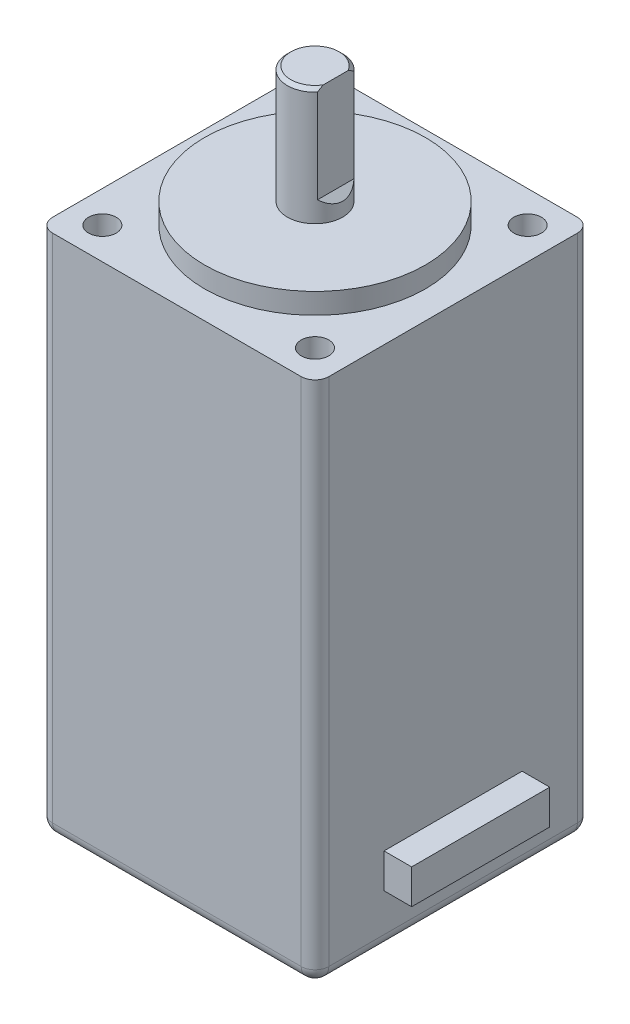
SolidWorks part; units mm, degrees
ref_plane "Front Plane" through (0, 0, 0) normal (0, 0, 1) x (1, 0, 0)
ref_plane "Top Plane" through (0, 0, 0) normal (0, 1, 0) x (1, 0, 0)
ref_plane "Right Plane" through (0, 0, 0) normal (1, 0, 0) x (0, 0, -1)
sketch "Sketch1" plane through (0, 0, 0) normal (0, 1, 0) x (1, 0, 0)
  line L1 (10, -10) -> (-10, -10)
  line L2 (10, -10) -> (10, 10)
  line L3 (10, 10) -> (-10, 10)
  line L4 (-10, -10) -> (-10, 10)
  line L5 (10, -10) -> (-10, 10) construction
  line L6 (10, 10) -> (-10, -10) construction
  point P0 (0, 0)
  dimension "D1" = 20
extrude "Boss-Extrude1" add sketch "Sketch1" against normal blind 38
sketch "Sketch2" plane through (0, 0, 0) normal (0, 1, 0) x (1, 0, 0)
  line L1 (7.7, -7.7) -> (-7.7, -7.7) construction
  line L2 (7.7, -7.7) -> (7.7, 7.7) construction
  line L3 (7.7, 7.7) -> (-7.7, 7.7) construction
  line L4 (-7.7, -7.7) -> (-7.7, 7.7) construction
  line L5 (7.7, -7.7) -> (-7.7, 7.7) construction
  line L6 (7.7, 7.7) -> (-7.7, -7.7) construction
  circle A0 centre (-7.7, 7.7) radius 1
  circle A1 centre (7.7, 7.7) radius 1
  circle A2 centre (7.7, -7.7) radius 1
  circle A3 centre (-7.7, -7.7) radius 1
  point P0 (0, 0)
  dimension "D4" = 2
  dimension "D2" = 15.4
extrude "Cut-Extrude1" cut sketch "Sketch2" against normal blind 2.5
sketch "Sketch3" plane through (0, 0, 0) normal (0, 1, 0) x (1, 0, 0)
  circle A0 centre (0, 0) radius 8
  dimension "D1" = 16
extrude "Boss-Extrude2" add sketch "Sketch3" along normal blind 1.5
sketch "Sketch4" plane through (0, 0, 0) normal (0, 1, 0) x (1, 0, 0)
  circle A0 centre (0, 0) radius 2
  dimension "D1" = 4
extrude "Boss-Extrude3" add sketch "Sketch4" along normal blind 10
sketch "Sketch5" plane through (0, 0, 0) normal (0, 0, 1) x (1, 0, 0)
  line L0 (2, 10) -> (1.5, 10)
  line L1 (2, 10) -> (-2, 10) construction
  line L2 (1.5, 10) -> (1.5, 3)
  line L3 (1.5, 3) -> (2, 2.5)
  line L4 (2, 1.5) -> (2, 10) construction
  line L5 (2, 2.5) -> (2, 10)
  dimension "D1" = 45
  dimension "D2" = 0.5
  dimension "D3" = 7.5
extrude "Cut-Extrude2" cut sketch "Sketch5" against normal through all both and the other way through all
chamfer "Chamfer1" distance 0.25 angle 45 1 edges at (-2, 10, 0)
fillet "Fillet1" radius 1 8 edges at (0, -38, 10) (10, -38, 0) (0, -38, -10) (-10, -38, 0) (-10, -19, -10) (10, -19, -10) (10, -19, 10) (-10, -19, 10)
sketch "Sketch6" plane through (0, 0, 0) normal (1, 0, 0) x (0, 0, -1)
  line L0 (0, -33) -> (0, 0) construction
  line L1 (5, -34.25) -> (-5, -34.25)
  line L2 (5, -34.25) -> (5, -31.75)
  line L3 (5, -31.75) -> (-5, -31.75)
  line L4 (-5, -34.25) -> (-5, -31.75)
  line L5 (5, -34.25) -> (-5, -31.75) construction
  line L6 (5, -31.75) -> (-5, -34.25) construction
  line L7 (9, -38) -> (-9, -38) construction
  point P0 (0, -33)
  dimension "D1" = 5
  dimension "D2" = 2.5
  dimension "D3" = 10
extrude "Boss-Extrude4" add sketch "Sketch6" along normal offset from surface (12 mm away) 2 up to face at (10, -18.5, 0) offset beyond the face yes
equation "\"D1@Sketch1\" = \"ARM Both Nema Width\""
equation "\"D1@Boss-Extrude1\" = \"ARM Both Nema Height\""
equation "\"D2@Sketch2\" = \"ARM Both Nema Bolt Off\""
equation "\"D4@Sketch2\" = \"ARM Both Nema Bolt Size\""
equation "\"D1@Cut-Extrude1\" = \"ARM Both Nema Bolt Depth\""
equation "\"D1@Sketch3\" = \"ARM Both Nema Center Dia 1\" - 1.0mm"
equation "\"D1@Boss-Extrude2\" = \"ARM Both Nema Center Height\""
equation "\"D1@Sketch4\" = \"ARM Both Nema Shaft Dia\""
equation "\"D1@Boss-Extrude3\"= \"ARM Both Nema Shaft Length\""
equation "\"D2@Sketch5\"= \"ARM Both Nema Shaft Dia\" * ( 1 / 8 )"
equation "\"D3@Sketch5\"= \"ARM Both Nema Shaft Length\" * ( 3 / 4 )"
equation "\"D1@Chamfer1\"= \"ALL Small Fillet\" / 2"
equation "\"ALL Big Fillet\"= 10.0mm"
equation "\"ALL Medium Fillet\"= 1.0mm"
equation "\"ALL Small Fillet\"= 0.5mm"
equation "\"BODY Rad\"= 82.5mm"
equation "\"BODY End Cut Rad\"= 72.5mm"
equation "\"BODY Height Ext\"= 27.5mm"
equation "\"BODY Bottom Cut Dist\"= 50.0mm"
equation "\"BODY Seal Thickness\"= 3.75mm"
equation "\"BODY Wall Extra Thickness\"= 2.5mm"
equation "\"BODY Bottom Extra Nut Wall\"= 7.5mm"
equation "\"ARM Both Dia\"= 39.75mm"
equation "\"ARM Both Length\"= 67.5mm"
equation "\"ARM Both Wire Hole Dia\"= 15.0mm"
equation "\"ARM Both Prop Seal Thickness\"= 2.5mm"
equation "\"ARM Both Brass Insert Dia\"= 4.875mm"
equation "\"ARM Both Bolt Cut Depth\"= 12.5mm"
equation "\"ARM Both Nema Bolt Off\"= 15.4mm"
equation "\"ARM Both Nema Bolt Depth\"= 2.5mm"
equation "\"ARM Both Nema Width\"= 20.0mm"
equation "\"ARM Both Nema Wall Off\"= 2.5mm"
equation "\"ARM Both Nema Center Dia 1\"= 17.0mm"
equation "\"ARM Both Nema Center Dia 2\"= 10.0mm"
equation "\"ARM Both Nema Bearing OD\"= 16.0mm"
equation "\"ARM Both Nema Bearing ID\"= 10.0mm"
equation "\"ARM Both Nema Bearing Thickness\"= 4.0mm"
equation "\"ARM Both Nema Height\"= 38.0mm"
equation "\"ARM Both Nema Shaft Dia\"= 4.0mm"
equation "\"ARM Both Nema Shaft Length\"= 10.0mm"
equation "\"ARM Both Nema Center Height\"= 1.5mm"
equation "\"ARM Rotating Bearing OD\"= 68.0mm"
equation "\"ARM Rotating Bearing ID\"= 40.0mm"
equation "\"ARM Rotating Bearing Thickness\"= 15.0mm"
equation "\"ARM Static Mount Dia\"= 65.0mm"
equation "\"ARM Static Bolt Off\"= 1.125mm"
equation "\"ALL Bolt Hole Off\"= 0.25mm"
equation "\"ALL Vert Bolt Hole Off Scalar\"= 0.5mm"
equation "\"ALL Horz Bolt Hole Off Scalar\"= 1.25mm"
equation "\"ALL Nut Size Off\"= 0.25mm"
equation "\"ALL Vert Nut Off Scalar\"= 0.5mm"
equation "\"ALL Horz Nut Off Scalar\"= 1.25mm"
equation "\"BODY Bolt Count\"= 12"
equation "\"BODY Bolt Size\"= 6"
equation "\"BODY Bolt Length\"= 22.0mm"
equation "\"BODY Bolt Head Dia\"= IIF ( \"BODY Bolt Size\" = 3 , 5.75mm , IIF ( \"BODY Bolt Size\" = 4 , 7.25mm , IIF ( \"BODY Bolt Size\" = 5 , 8.75mm , IIF ( \"BODY Bolt Size\" = 6 , 10.25mm , 5.75mm ) ) ) )"
equation "\"BODY Bolt Head Height\"= IIF ( \"BODY Bolt Size\" = 3 , 3.0mm , IIF ( \"BODY Bolt Size\" = 4 , 4.0mm , IIF ( \"BODY Bolt Size\" = 5 , 5.0mm , IIF ( \"BODY Bolt Size\" = 6 , 6.0mm , 3.0mm ) ) ) )"
equation "\"BODY Nut Width\"= IIF ( \"BODY Bolt Size\" = 3 , 5.5mm , IIF ( \"BODY Bolt Size\" = 4 , 7.0mm , IIF ( \"BODY Bolt Size\" = 5 , 8.0mm , IIF ( \"BODY Bolt Size\" = 6 , 10.0mm , 5.5mm ) ) ) )"
equation "\"BODY Nut Height\"= IIF ( \"BODY Bolt Size\" = 3 , 4.0mm , IIF ( \"BODY Bolt Size\" = 4 , 5.0mm , IIF ( \"BODY Bolt Size\" = 5 , 5.0mm , IIF ( \"BODY Bolt Size\" = 6 , 6.0mm , 4.0mm ) ) ) )"
equation "\"ARM Static Bolt Count\"= 8"
equation "\"ARM Static Bolt Size\"= 5"
equation "\"ARM Static Bolt Length\"= 20.0mm"
equation "\"ARM Static Bolt Head Dia\"= IIF ( \"ARM Static Bolt Size\" = 3 , 5.75mm , IIF ( \"ARM Static Bolt Size\" = 4 , 7.25mm , IIF ( \"ARM Static Bolt Size\" = 5 , 8.75mm , IIF ( \"ARM Static Bolt Size\" = 6 , 10.25mm , 5.75mm ) ) ) )"
equation "\"ARM Static Bolt Head Height\"= IIF ( \"ARM Static Bolt Size\" = 3 , 3.0mm , IIF ( \"ARM Static Bolt Size\" = 4 , 4.0mm , IIF ( \"ARM Static Bolt Size\" = 5 , 5.0mm , IIF ( \"ARM Static Bolt Size\" = 6 , 6.0mm , 3.0mm ) ) ) )"
equation "\"ARM Static Nut Width\"= IIF ( \"ARM Static Bolt Size\" = 3 , 5.5mm , IIF ( \"ARM Static Bolt Size\" = 4 , 7.0mm , IIF ( \"ARM Static Bolt Size\" = 5 , 8.0mm , IIF ( \"ARM Static Bolt Size\" = 6 , 10.0mm , 5.5mm ) ) ) )"
equation "\"ARM Static Nut Height\"= IIF ( \"ARM Static Bolt Size\" = 3 , 4.0mm , IIF ( \"ARM Static Bolt Size\" = 4 , 5.0mm , IIF ( \"ARM Static Bolt Size\" = 5 , 5.0mm , IIF ( \"ARM Static Bolt Size\" = 6 , 6.0mm , 4.0mm ) ) ) )"
equation "\"ARM Gear Width\"= 10.0mm"
equation "\"ARM Gear Width Off\"= 2.5mm"
equation "\"ARM Gear Bolt Count\"= 4"
equation "\"ARM Gear Rotation\"= 360.0deg"
equation "\"ARM Gear Bolt Size\"= 3"
equation "\"ARM Gear Bolt Length\"= 20.0mm"
equation "\"ARM Gear Bolt Head Dia\"= IIF ( \"ARM Static Bolt Size\" = 3 , 5.75mm , IIF ( \"ARM Static Bolt Size\" = 4 , 7.25mm , IIF ( \"ARM Static Bolt Size\" = 5 , 8.75mm , IIF ( \"ARM Static Bolt Size\" = 6 , 10.25mm , 5.75mm ) ) ) )"
equation "\"ARM Gear Bolt Head Height\"= IIF ( \"ARM Static Bolt Size\" = 3 , 3.0mm , IIF ( \"ARM Static Bolt Size\" = 4 , 4.0mm , IIF ( \"ARM Static Bolt Size\" = 5 , 5.0mm , IIF ( \"ARM Static Bolt Size\" = 6 , 6.0mm , 3.0mm ) ) ) )"
equation "\"ARM Gear Nut Width\"= IIF ( \"ARM Static Bolt Size\" = 3 , 5.5mm , IIF ( \"ARM Static Bolt Size\" = 4 , 7.0mm , IIF ( \"ARM Static Bolt Size\" = 5 , 8.0mm , IIF ( \"ARM Static Bolt Size\" = 6 , 10.0mm , 5.5mm ) ) ) )"
equation "\"ARM Gear Nut Height\"= IIF ( \"ARM Static Bolt Size\" = 3 , 4.0mm , IIF ( \"ARM Static Bolt Size\" = 4 , 5.0mm , IIF ( \"ARM Static Bolt Size\" = 5 , 5.0mm , IIF ( \"ARM Static Bolt Size\" = 6 , 6.0mm , 4.0mm ) ) ) )"
equation "\"ARM Both Prop Plate Bolt Size\"= 3"
equation "\"ARM Both Prop Plate Bolt Length\"= 16.0mm"
equation "\"ARM Both Prop Plate Bolt Head Dia\"= IIF ( \"ARM Both Prop Plate Bolt Size\" = 3 , 5.75mm , IIF ( \"ARM Both Prop Plate Bolt Size\" = 4 , 7.25mm , IIF ( \"ARM Both Prop Plate Bolt Size\" = 5 , 8.75mm , IIF ( \"ARM Both Prop Plate Bolt Size\" = 6 , 10.25mm , 5.75mm ) ) ) )"
equation "\"ARM Both Prop Plate Bolt Head Height\"= IIF ( \"ARM Both Prop Plate Bolt Size\" = 3 , 3.0mm , IIF ( \"ARM Both Prop Plate Bolt Size\" = 4 , 4.0mm , IIF ( \"ARM Both Prop Plate Bolt Size\" = 5 , 5.0mm , IIF ( \"ARM Both Prop Plate Bolt Size\" = 6 , 6.0mm , 3.0mm ) ) ) )"
equation "\"ARM Both Nema Bolt Size\"= 2"
equation "\"ARM Both Nema Bolt Head Dia\"= IIF ( \"ARM Both Nema Bolt Size\" = 3 , 5.75mm , IIF ( \"ARM Both Nema Bolt Size\" = 4 , 7.25mm , IIF ( \"ARM Both Nema Bolt Size\" = 5 , 8.75mm , IIF ( \"ARM Both Nema Bolt Size\" = 6 , 10.25mm , 5.75mm ) ) ) )"
equation "\"ARM Both Nema Bolt Head Height\"= IIF ( \"ARM Both Nema Bolt Size\" = 3 , 3.0mm , IIF ( \"ARM Both Nema Bolt Size\" = 4 , 4.0mm , IIF ( \"ARM Both Nema Bolt Size\" = 5 , 5.0mm , IIF ( \"ARM Both Nema Bolt Size\" = 6 , 6.0mm , 3.0mm ) ) ) )"
